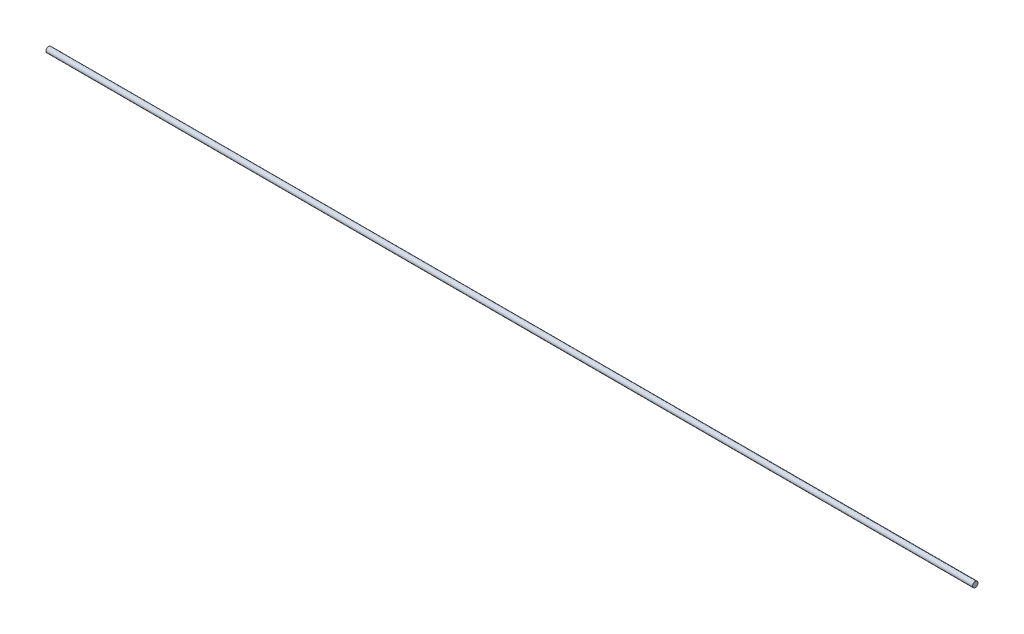
SolidWorks part; units mm, degrees
ref_plane "Front Plane" through (0, 0, 0) normal (0, 0, 1) x (1, 0, 0)
ref_plane "Top Plane" through (0, 0, 0) normal (0, 1, 0) x (1, 0, 0)
ref_plane "Right Plane" through (0, 0, 0) normal (1, 0, 0) x (0, 0, -1)
sketch "Sketch1" plane through (0, 0, 0) normal (1, 0, 0) x (0, 0, -1)
  circle A0 centre (0, 0) radius 0.003
  circle A1 centre (0, 0) radius 3
extrude "Boss-Extrude1" add sketch "Sketch1" along normal mid plane 1022
